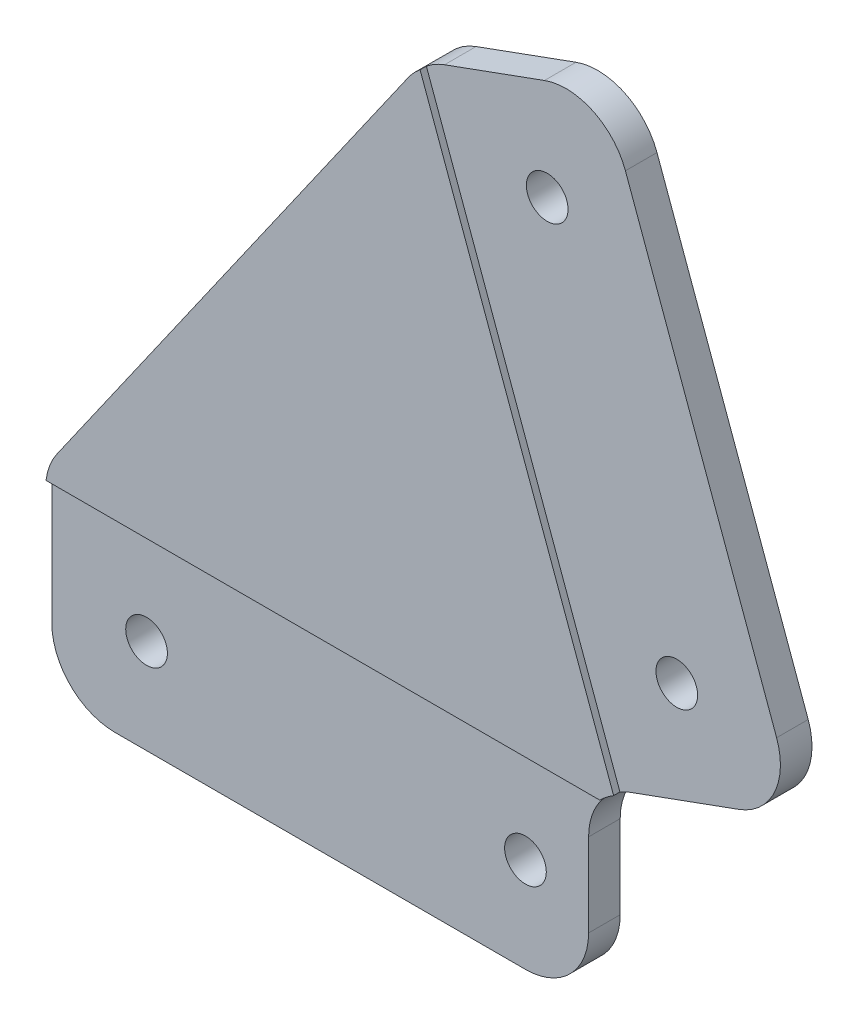
SolidWorks part; units mm, degrees
material "3.1325 (EN-AW 2017A)"
ref_plane "正面" through (0, 0, 0) normal (0, 0, 1) x (1, 0, 0)
ref_plane "平面" through (0, 0, 0) normal (0, 1, 0) x (1, 0, 0)
ref_plane "右側面" through (0, 0, 0) normal (1, 0, 0) x (0, 0, -1)
sketch "ｽｹｯﾁ1" plane through (0, 0, 0) normal (0, 0, 1) x (1, 0, 0)
  line L0 (0, 0) -> (306.8848, 365.731) construction
  line L1 (306.8848, 365.731) -> (440, 0) construction
  line L2 (440, 0) -> (0, 0) construction
  line L3 (306.8848, 365.731) -> (306.8848, 0) construction
  line L4 (306.8848, 365.731) -> (0, 0) construction
  line L9 (306.8848, 365.731) -> (295.3941, 375.3729)
  line L20 (440, 0) -> (395, 0)
  line L21 (440, 0) -> (440, -16)
  line L22 (395, 0) -> (395, -16)
  line L23 (440, -16) -> (395, -16)
  line L24 (440, 0) -> (424.6091, 42.2862)
  line L25 (440, 0) -> (454.0954, 5.1303)
  line L26 (424.6091, 42.2862) -> (438.7045, 47.4165)
  line L27 (454.0954, 5.1303) -> (438.7045, 47.4165)
  line L28 (424.6091, 42.2862) -> (395, 0)
  line L29 (440, 0) -> (437.5, -0.9099)
  line L30 (437.5, -0.9099) -> (437.5, -16)
  dimension "D4" = 16
  dimension "D5" = 15
  dimension "D6" = 45
  dimension "D1" = 440
  dimension "D2" = 70
  dimension "D3" = 50
  dimension "D7" = 45
  dimension "D8" = 2.5
extrude "ﾎﾞｽ - 押し出し1" add sketch "ｽｹｯﾁ1" along normal blind 3
sketch "ｽｹｯﾁ2" plane through (0, 0, 3) normal (0, 0, 1) x (1, 0, 0)
  line L6 (437.5, -16) -> (395, -16) construction
  line L7 (395, 0) -> (395, -16) construction
  line L8 (437.5, -0.9099) -> (454.0954, 5.1303) construction
  line L9 (424.6091, 42.2862) -> (438.7045, 47.4165) construction
  line L10 (454.0954, 5.1303) -> (438.7045, 47.4165) construction
  circle A4 centre (402.5, -8.5) radius 1.65
  circle A5 centre (432.5, -8.5) radius 1.65
  circle A6 centre (434.2219, 37.8036) radius 1.65
  circle A7 centre (444.4825, 9.6128) radius 1.65
  dimension "D1" = 3.3
  dimension "D2" = 3.3
  dimension "D3" = 3.3
  dimension "D4" = 3.3
  dimension "D5" = 7.5
  dimension "D6" = 7.5
  dimension "D7" = 7.5
  dimension "D8" = 30
  dimension "D9" = 7.5
  dimension "D10" = 7.5
  dimension "D11" = 7.5
  dimension "D12" = 7.5
extrude "ｶｯﾄ - 押し出し1" cut sketch "ｽｹｯﾁ2" against normal blind 3
fillet "ﾌｨﾚｯﾄ1" radius 5 7 edges at (454.0954, 5.1303, 1.5) (395, -16, 1.5) (438.7045, 47.4165, 1.5) (424.6091, 42.2862, 1.5) (395, 0, 1.5) (437.5, -0.9099, 1.5) (437.5, -16, 1.5)
sketch "ｽｹｯﾁ4" plane through (0, 0, 3) normal (0, 0, 1) x (1, 0, 0)
  line L0 (438.7045, 47.4165) -> (454.4374, 4.1906)
  line L1 (438.7045, 47.4165) -> (424.5621, 42.2691)
  line L2 (454.4374, 4.1906) -> (440.295, -0.9568)
  line L3 (424.5621, 42.2691) -> (440.295, -0.9568)
  line L4 (452.3853, 9.8288) -> (440.4146, 42.718) construction
  line L5 (395, -16) -> (439.5, -16)
  line L6 (395, -16) -> (395, -0.95)
  line L7 (439.5, -16) -> (439.5, -0.95)
  line L8 (395, -0.95) -> (439.5, -0.95)
  line L9 (432.5, -16) -> (400, -16) construction
  line L10 (426.0905, 42.8254) -> (434.006, 45.7064) construction
  line L11 (395, -1.5765) -> (395, -11) construction
  line L12 (437.5, -4.411) -> (437.5, -11) construction
  line L13 (449.3969, 3.4202) -> (440.7899, 0.2875) construction
  point P20 (447.3662, 1.6169)
  dimension "D1" = 15.05
  dimension "D2" = 15.05
  dimension "D3" = 2
  dimension "D4" = 1
extrude "ｶｯﾄ - 押し出し2" cut sketch "ｽｹｯﾁ4" against normal blind 0.5
